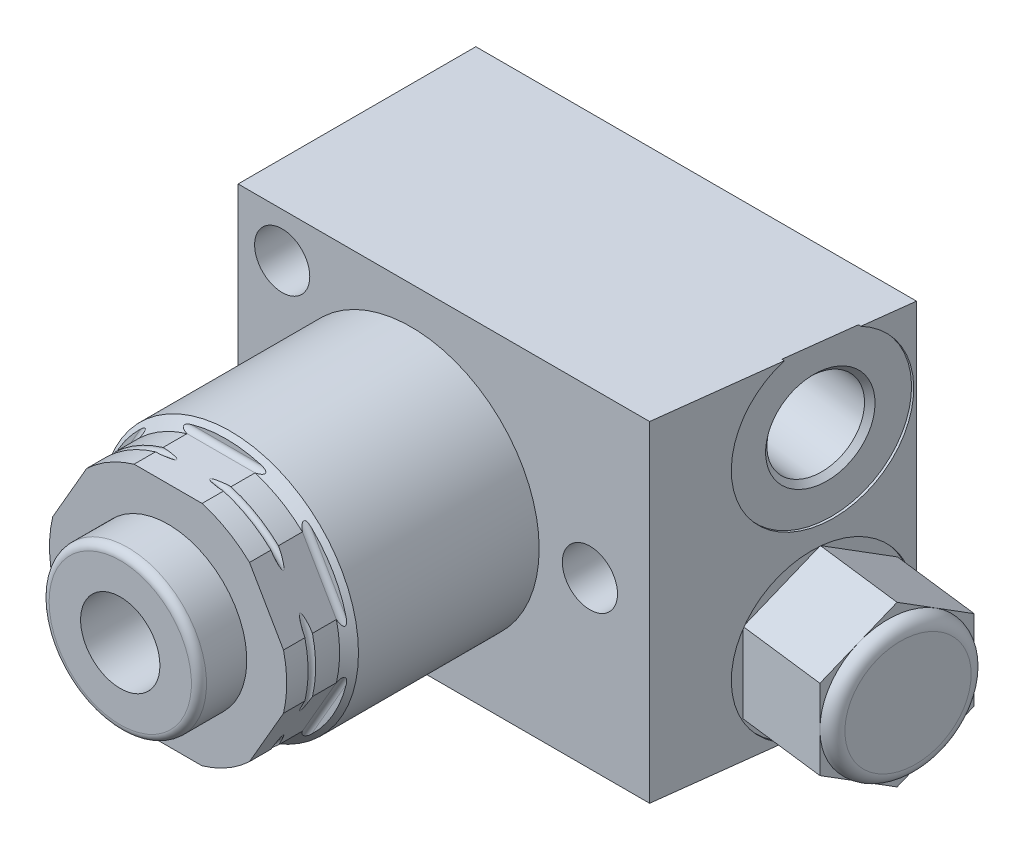
SolidWorks part; units mm, degrees
material "Alloy Steel"
ref_plane "Front Plane" through (0, 0, 0) normal (0, 0, 1) x (1, 0, 0)
ref_plane "Top Plane" through (0, 0, 0) normal (0, 1, 0) x (1, 0, 0)
ref_plane "Right Plane" through (0, 0, 0) normal (1, 0, 0) x (0, 0, -1)
sketch "Sketch1" plane through (0, 0, 0) normal (1, 0, 0) x (0, 0, -1)
  line L0 (0, 0) -> (122.3375, 0) construction
  line L1 (0, 0) -> (0, 10.9347)
  line L2 (0, 10.9347) -> (-2.5908, 10.9347)
  line L3 (-2.5908, 10.9347) -> (-2.5908, 12.0396)
  line L6 (-2.5908, 12.0396) -> (-7.239, 12.0396)
  line L7 (-7.239, 12.0396) -> (-8.1153, 12.9159)
  line L8 (-8.1153, 12.9159) -> (-33.7185, 12.9159)
  line L9 (-33.7185, 12.9159) -> (-34.671, 11.9634)
  line L10 (-34.671, 11.9634) -> (-40.005, 11.9634)
  line L11 (-40.005, 11.9634) -> (-40.005, 0)
  line L12 (0, 0) -> (-40.005, 0)
  dimension "D1" = 21.8694
  dimension "D2" = 2.5908
  dimension "D5" = 24.0792
  dimension "D6" = 7.239
  dimension "D7" = 25.8318
  dimension "D8" = 45
  dimension "D9" = 40.005
  dimension "D10" = 23.9268
  dimension "D11" = 45
  dimension "D12" = 5.334
revolve "Revolve1" add sketch "Sketch1" angle 360 about L0
sketch "Sketch2" plane through (0, 0, 0) normal (1, 0, 0) x (0, 0, -1)
  line L0 (0, 0) -> (-47.105, 0) construction
  line L1 (-40.005, 11.4617) -> (-34.671, 11.4617)
  line L2 (-40.005, 11.9634) -> (-40.005, -11.9634) construction
  line L3 (-34.163, 11.9697) -> (-34.163, 14.6367)
  line L4 (-34.163, 14.6367) -> (-40.005, 14.6367)
  line L5 (-40.005, 14.6367) -> (-40.005, 11.4617)
  arc A0 (-34.163, 11.9697) -> (-34.671, 11.4617) centre (-34.671, 11.9697) cw
  dimension "D4" = 0.508
  dimension "D1" = 22.9235
  dimension "D2" = 5.842
  dimension "D3" = 3.175
extrude "Cut-Extrude1" cut sketch "Sketch2" against normal through all and the other way through all
pattern_circular "CirPattern1" count 6 over 360 about axis through (0, 0, 0) along (0, 0, 1) of "Cut-Extrude1"
sketch "Sketch6" plane through (0, 0, 0) normal (0, 1, 0) x (1, 0, 0)
  line L0 (-17.4498, -15.494) -> (24.0561, -15.494)
  line L1 (24.0561, -15.494) -> (27.0002, 8.4836)
  line L2 (27.0002, 8.4836) -> (-17.4498, 8.4836)
  line L3 (-17.4498, 8.4836) -> (-17.4498, -15.494)
  line L4 (3.428, -40.005) -> (-3.428, -40.005) construction
  dimension "D1" = 24.511
  dimension "D2" = 83
  dimension "D3" = 23.9776
  dimension "D4" = 44.45
  dimension "D5" = 17.4498
extrude "Extrude1" add sketch "Sketch6" along normal mid plane 33.3502
sketch "Sketch3" plane through (0, 0, 0) normal (1, 0, 0) x (0, 0, -1)
  line L0 (0, 0) -> (-60.8041, 0) construction
  line L1 (-44.831, 0) -> (-44.831, 7.1755)
  line L2 (-44.069, 7.9375) -> (-40.005, 7.9375)
  line L3 (-40.005, 2.7621) -> (-40.005, 8.6996) construction
  line L4 (-40.005, 7.9375) -> (-40.005, 0)
  line L5 (-40.005, 2.7621) -> (-40.005, -2.7621) construction
  line L6 (-40.005, 0) -> (-44.831, 0)
  line L9 (8.4836, 16.6751) -> (8.4836, -16.6751) construction
  arc A0 (-44.069, 7.9375) -> (-44.831, 7.1755) centre (-44.069, 7.1755) ccw
  dimension "D1" = 0.762
  dimension "D2" = 15.875
  dimension "D3" = 53.3146
revolve "Revolve2" add sketch "Sketch3" angle 360 about L0
sketch "Sketch4" plane through (0, 0, 44.831) normal (0, 0, 1) x (1, 0, 0)
  circle A0 centre (0, 0) radius 4.0005
  circle A1 centre (0, 0) radius 7.9375 construction
  dimension "D1" = 8.001
extrude "Cut-Extrude2" cut sketch "Sketch4" against normal blind 10.541
sketch "Sketch5" plane through (0, 0, 0) normal (1, 0, 0) x (0, 0, -1)
  line L0 (-40.005, 11.4617) -> (-40.005, 8.6996) construction
  line L1 (0, 0) -> (-52.6213, 0) construction
  line L2 (-37.846, 15.1384) -> (-37.846, 11.9634)
  line L3 (-37.084, 15.1384) -> (-37.084, 11.9634)
  line L4 (-37.846, 15.1384) -> (-37.084, 15.1384)
  arc A0 (-37.846, 11.9634) -> (-37.084, 11.9634) centre (-37.465, 11.9634) ccw
  dimension "D3" = 0.762
  dimension "D1" = 2.54
  dimension "D2" = 11.9634
  dimension "D4" = 3.175
revolve "Cut-Revolve1" cut sketch "Sketch5" angle 360 about L1
hole_wizard "Hole1" positions "Sketch8" profile "Sketch7" legacy end condition up to next
sketch "Sketch8" plane through (0, 0, 15.494) normal (0, 0, 1) x (1, 0, 0)
  line L0 (0, 0) -> (0, 25.169) construction
  line L1 (0, 0) -> (-25.7102, 0) construction
  point P0 (-13.0048, 12.192)
  point P9 (-13.0048, -12.192)
  point P10 (18.034, 0)
  dimension "D1" = 12.192
  dimension "D2" = 13.0048
  dimension "D3" = 18.034
sketch "Sketch7" plane through (-13.0048, 12.192, 15.494) normal (1, 0, 0) x (0, -1, 0)
  line L0 (0, 0) -> (0, 23.9776)
  line L1 (0, 23.9776) -> (2.7815, 23.9776)
  line L2 (2.7815, 23.9776) -> (2.7815, 0)
  line L3 (2.7815, 0) -> (0, 0)
  line L4 (0, 110) -> (0, -10) construction
  dimension "Diameter" = 5.563
  dimension "Depth" = 23.9776
ref_plane "Plane1" through (0, -9.1821, 0) normal (0, 1, 0) x (-1, 0, 0)
sketch "Sketch9" plane through (0, -9.1821, 0) normal (0, 1, 0) x (-1, 0, 0)
  line L0 (-25.9632, -0.038) -> (-18.6103, -0.9409) construction
  line L1 (-24.0561, 15.494) -> (-27.0002, -8.4836) construction
  line L2 (-24.9572, 8.1554) -> (-24.7051, 8.1245)
  line L3 (-24.7051, 8.1245) -> (-25.1075, 4.8471)
  line L4 (-25.1075, 4.8471) -> (-24.6431, 4.2527)
  line L5 (-24.6431, 4.2527) -> (-14.6849, 3.03)
  line L6 (-14.6849, 3.03) -> (-15.2235, -1.3567)
  line L7 (-15.2235, -1.3567) -> (-25.9632, -0.038)
  line L8 (-25.9632, -0.038) -> (-24.9572, 8.1554)
  dimension "D1" = 8.509
  dimension "D2" = 16.51
  dimension "D3" = 0.254
  dimension "D4" = 8.8392
  dimension "D5" = 10.5664
  dimension "D6" = 45
  dimension "D7" = 9.906
revolve "Cut-Revolve2" cut sketch "Sketch9" angle 360 about L0
pattern_linear "LPattern1" count 2 spacing 18.3642 along (0, 1, 0) of "Cut-Revolve2"
sketch "Sketch10" plane through (25.3209, 0, 3.109) normal (0.9925, 0, 0.1219) x (0.1219, 0, -0.9925)
  line L1 (10.1869, -13.2149) -> (10.1869, -5.1493)
  line L2 (10.1869, -5.1493) -> (3.2019, -1.1165)
  line L3 (3.2019, -1.1165) -> (-3.7831, -5.1493)
  line L4 (-3.7831, -5.1493) -> (-3.7831, -13.2149)
  line L5 (-3.7831, -13.2149) -> (3.2019, -17.2477)
  line L6 (3.2019, -17.2477) -> (10.1869, -13.2149)
  circle A0 centre (3.2019, -9.1821) radius 6.985 construction
  dimension "D1" = 13.97
extrude "Extrude2" add sketch "Sketch10" along normal blind 10.16
sketch "Sketch11" plane through (0, -9.1821, 0) normal (0, 1, 0) x (-1, 0, 0)
  line L0 (-35.7954, 1.1692) -> (-34.9441, 8.1021) construction
  line L1 (-34.9441, 8.1021) -> (-24.8598, 6.864) construction
  line L2 (-35.7954, 1.1692) -> (-35.0989, 6.8416) construction
  line L3 (-33.6836, 7.9474) -> (-24.8598, 6.864) construction
  line L4 (-33.6836, 7.9474) -> (-33.0645, 12.9895)
  line L5 (-52.2153, 3.1853) -> (-22.674, -0.4419) construction
  line L6 (-15.2235, -1.3567) -> (-25.1817, -0.134) construction
  line L7 (-35.0989, 6.8416) -> (-36.9897, 7.0738)
  line L8 (-33.0645, 12.9895) -> (-36.2158, 13.3764)
  line L9 (-36.9897, 7.0738) -> (-36.2158, 13.3764)
  arc A0 (-35.0989, 6.8416) -> (-33.6836, 7.9474) centre (-33.8384, 6.6868) cw
  dimension "D1" = 1.27
  dimension "D2" = 6.35
  dimension "D3" = 3.175
revolve "Cut-Revolve3" cut sketch "Sketch11" angle 360 about L5
